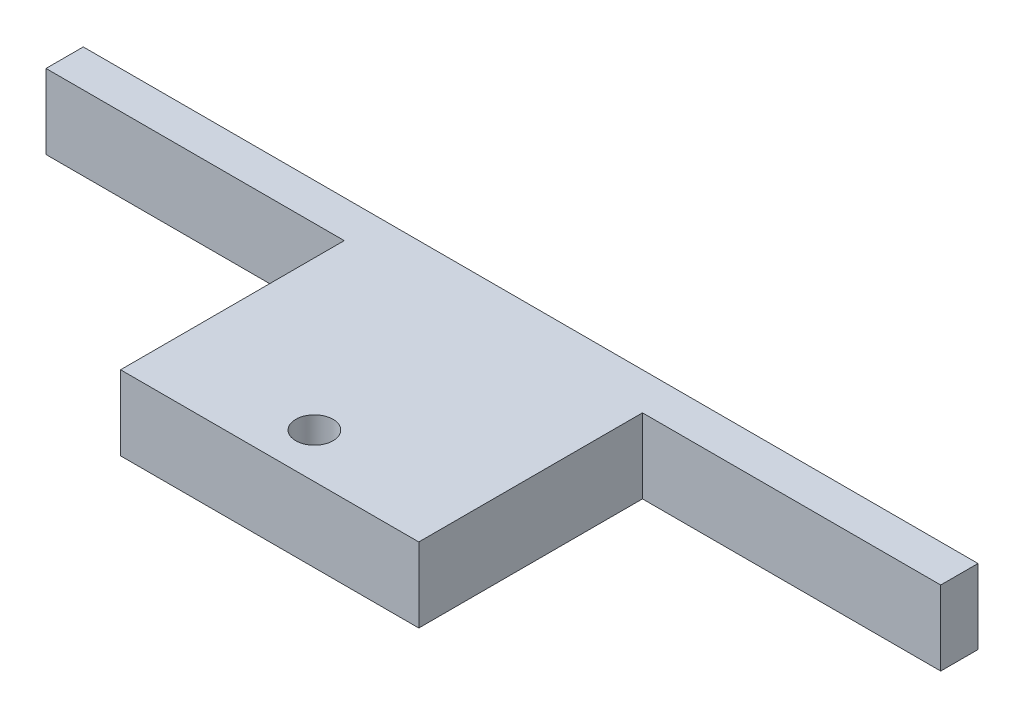
SolidWorks part; units mm, degrees
ref_plane "Front Plane" through (0, 0, 0) normal (0, 0, 1) x (1, 0, 0)
ref_plane "Top Plane" through (0, 0, 0) normal (0, 1, 0) x (1, 0, 0)
ref_plane "Right Plane" through (0, 0, 0) normal (1, 0, 0) x (0, 0, -1)
sketch "Sketch1" plane through (0, 0, 0) normal (0, 1, 0) x (1, 0, 0)
  line L1 (0, 0) -> (152.4, 0)
  line L2 (0, 0) -> (0, 114.3)
  line L3 (0, 114.3) -> (152.4, 114.3)
  line L4 (152.4, 0) -> (152.4, 114.3)
  dimension "D1" = 152.4
  dimension "D2" = 114.3
extrude "Boss-Extrude1" add sketch "Sketch1" along normal blind 38.1 contours L2 L3 L4 L1
sketch "Sketch2" plane through (0, 0, -114.3) normal (0, 0, -1) x (-1, 0, 0)
  line L0 (0, 38.1) -> (0, 0) construction
  line L1 (152.4, 38.1) -> (-304.8, 38.1)
  line L2 (152.4, 38.1) -> (152.4, 0)
  line L3 (152.4, 0) -> (-304.8, 0)
  line L4 (-304.8, 38.1) -> (-304.8, 0)
  dimension "D1" = 457.2
  dimension "D2" = 152.4
extrude "Boss-Extrude2" add sketch "Sketch2" along normal blind 19.05
hole_wizard "#96 (0.0063) Diameter Hole1" positions "3DSketch1" profile "Sketch5" hole size "#96" standard "ANSI Inch" end condition through all
sketch3d "3DSketch1"
  line L0 (152.4, 0, 0) -> (152.4, 0, -114.3) construction
  line L1 (304.8, 0, -133.35) -> (-152.4, 0, -133.35) construction
  point P0 (76.2, 0, -22.86)
  dimension "D1" = 76.2
  dimension "D2" = 110.49
sketch "Sketch5" plane through (76.2, 0, -22.86) normal (1, 0, 0) x (0, 0, -1)
  line L0 (0, 0) -> (0, 38.1)
  line L1 (0, 38.1) -> (9.525, 38.1)
  line L2 (9.525, 38.1) -> (9.525, 0)
  line L5 (9.525, 0) -> (0, 0)
  line L11 (0, -6.35) -> (0, 107.95) construction
  dimension "Thru Hole Dia." = 19.05
  dimension "Thru Hole Depth" = 38.1
